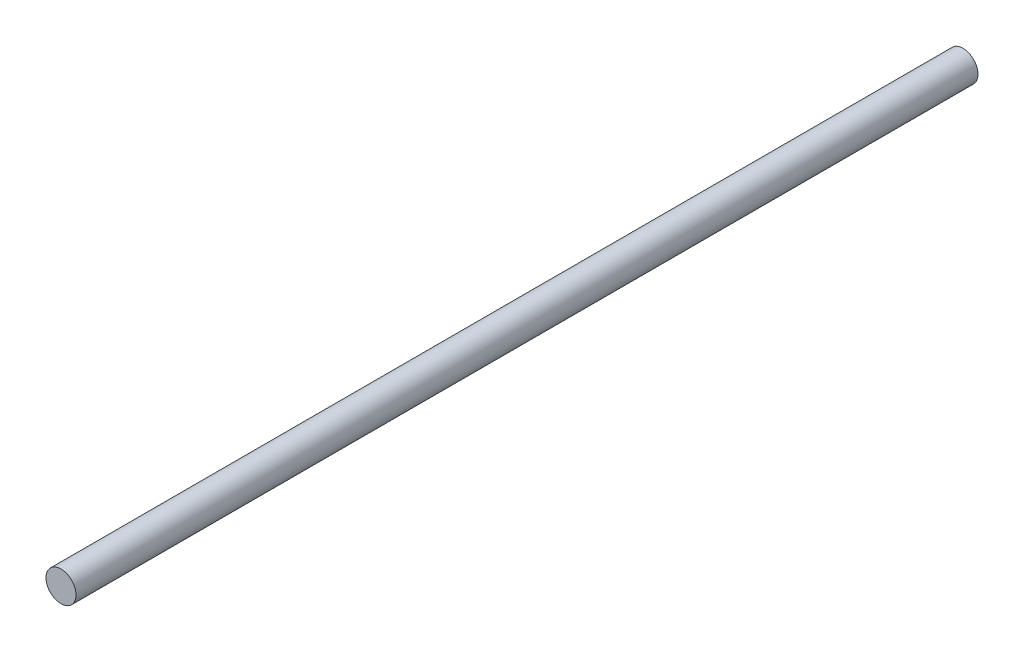
SolidWorks part; units mm, degrees
ref_plane "Front Plane" through (0, 0, 0) normal (0, 0, 1) x (1, 0, 0)
ref_plane "Top Plane" through (0, 0, 0) normal (0, 1, 0) x (1, 0, 0)
ref_plane "Right Plane" through (0, 0, 0) normal (1, 0, 0) x (0, 0, -1)
sketch "Sketch1" plane through (0, 0, 0) normal (0, 0, 1) x (1, 0, 0)
  circle A0 centre (0, 0) radius 12.7
  dimension "D1" = 25.4
extrude "Boss-Extrude1" add sketch "Sketch1" along normal blind 762
